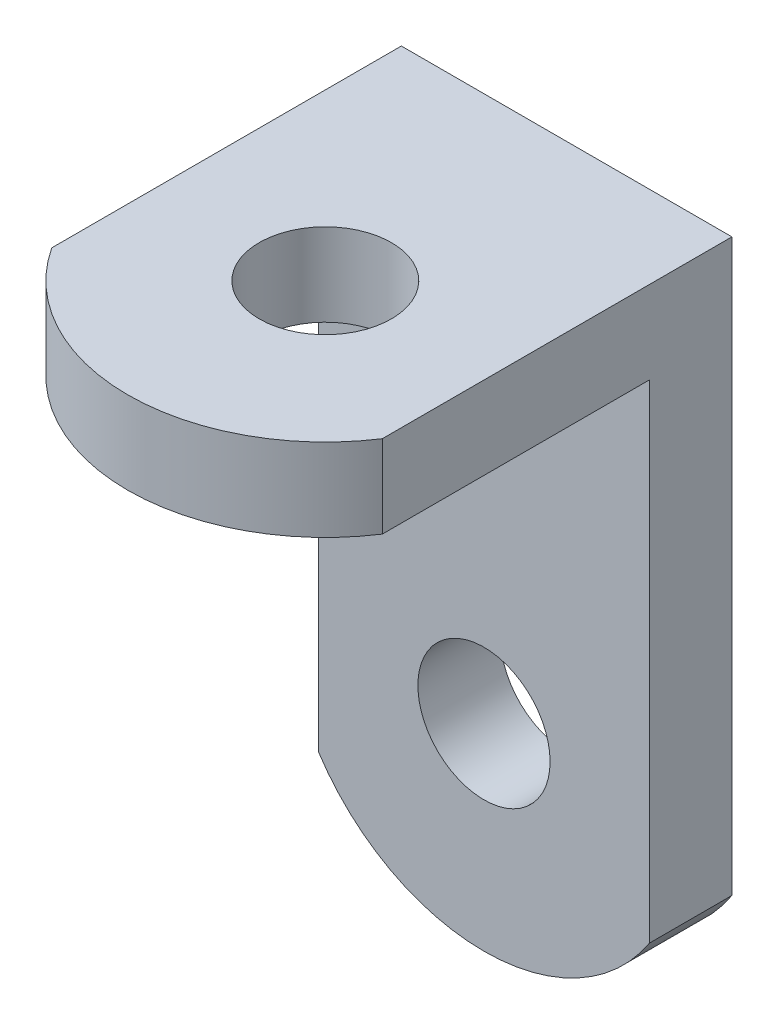
SolidWorks part; units mm, degrees
ref_plane "Front Plane" through (0, 0, 0) normal (0, 0, 1) x (1, 0, 0)
ref_plane "Top Plane" through (0, 0, 0) normal (0, 1, 0) x (1, 0, 0)
ref_plane "Right Plane" through (0, 0, 0) normal (1, 0, 0) x (0, 0, -1)
sketch "Sketch1" plane through (0, 0, 0) normal (0, 1, 0) x (1, 0, 0)
  line L1 (-22.7773, 14.8085) -> (-10.0773, 14.8085)
  line L2 (-22.7773, 14.8085) -> (-22.7773, -2.0825)
  line L3 (-22.7773, -2.0825) -> (-10.0773, -2.0825)
  line L4 (-10.0773, 14.8085) -> (-10.0773, -2.0825)
  line L5 (-22.7773, 14.8085) -> (-10.0773, -2.0825) construction
  line L6 (-22.7773, -2.0825) -> (-10.0773, 14.8085) construction
  point P0 (-16.4273, 6.363)
  dimension "D1" = 12.7
  dimension "D2" = 16.891
  dimension "D3" = 10.0773
  dimension "D4" = 6.363
extrude "Boss-Extrude1" add sketch "Sketch1" along normal blind 3.175
sketch "Sketch2" plane through (0, 3.175, 0) normal (0, 1, 0) x (1, 0, 0)
  line L0 (-22.7773, 5.5375) -> (-10.0773, 5.5375) construction
  line L1 (-22.7773, 14.8085) -> (-22.7773, -2.0825) construction
  line L2 (-10.0773, -2.0825) -> (-10.0773, 14.8085) construction
  line L3 (-22.7773, -2.0825) -> (-10.0773, -2.0825) construction
  circle A0 centre (-16.4273, 5.5375) radius 2.54
  dimension "D2" = 5.08
  dimension "D1" = 7.62
extrude "Cut-Extrude1" cut sketch "Sketch2" against normal through all
sketch "Sketch3" plane through (0, 0, 0) normal (0, -1, 0) x (1, 0, 0)
  line L0 (-22.7773, -14.8085) -> (-22.7773, 2.0825) construction
  line L1 (-10.0773, -14.8085) -> (-22.7773, -14.8085)
  line L2 (-10.0773, -14.8085) -> (-10.0773, -11.6335)
  line L3 (-10.0773, -11.6335) -> (-22.7773, -11.6335)
  line L4 (-22.7773, -14.8085) -> (-22.7773, -11.6335)
  dimension "D1" = 3.175
extrude "Boss-Extrude2" add sketch "Sketch3" along normal blind 22.225
sketch "Sketch4" plane through (0, 0, -11.6335) normal (0, 0, 1) x (1, 0, 0)
  line L0 (-10.0773, -14.605) -> (-22.7773, -14.605) construction
  line L1 (-10.0773, -22.225) -> (-10.0773, 0) construction
  line L2 (-22.7773, -22.225) -> (-22.7773, 0) construction
  line L3 (-10.0773, -22.225) -> (-22.7773, -22.225) construction
  circle A0 centre (-16.4273, -14.605) radius 2.54
  dimension "D2" = 5.08
  dimension "D1" = 7.62
extrude "Cut-Extrude2" cut sketch "Sketch4" against normal through all
sketch "Sketch6" plane through (0, 0, -11.6335) normal (0, 0, 1) x (1, 0, 0)
  line L1 (-10.0773, -22.225) -> (-22.7773, -22.225)
  line L2 (-22.7773, -22.225) -> (-22.7773, -18.7399)
  line L3 (-10.0773, -18.7399) -> (-10.0773, -22.225)
  line L4 (-22.7773, -22.225) -> (-22.7773, 0) construction
  line L5 (-10.0773, -22.225) -> (-10.0773, 0) construction
  arc A0 (-22.7773, -18.7399) -> (-10.0773, -18.7399) centre (-16.4273, -14.605) ccw
  dimension "D1" = 7.5776
extrude "Cut-Extrude3" cut sketch "Sketch6" against normal through all
sketch "Sketch7" plane through (0, 0, 0) normal (0, -1, 0) x (1, 0, 0)
  line L0 (-22.7773, -1.3767) -> (-22.7773, 2.0825)
  line L1 (-22.7773, -11.6335) -> (-22.7773, 2.0825) construction
  line L2 (-22.7773, 2.0825) -> (-10.0773, 2.0825)
  line L3 (-10.0773, 2.0825) -> (-10.0773, -1.3767)
  line L4 (-10.0773, 2.0825) -> (-10.0773, -11.6335) construction
  arc A0 (-10.0773, -1.3767) -> (-22.7773, -1.3767) centre (-16.4273, -5.5375) ccw
extrude "Cut-Extrude4" cut sketch "Sketch7" against normal through all
